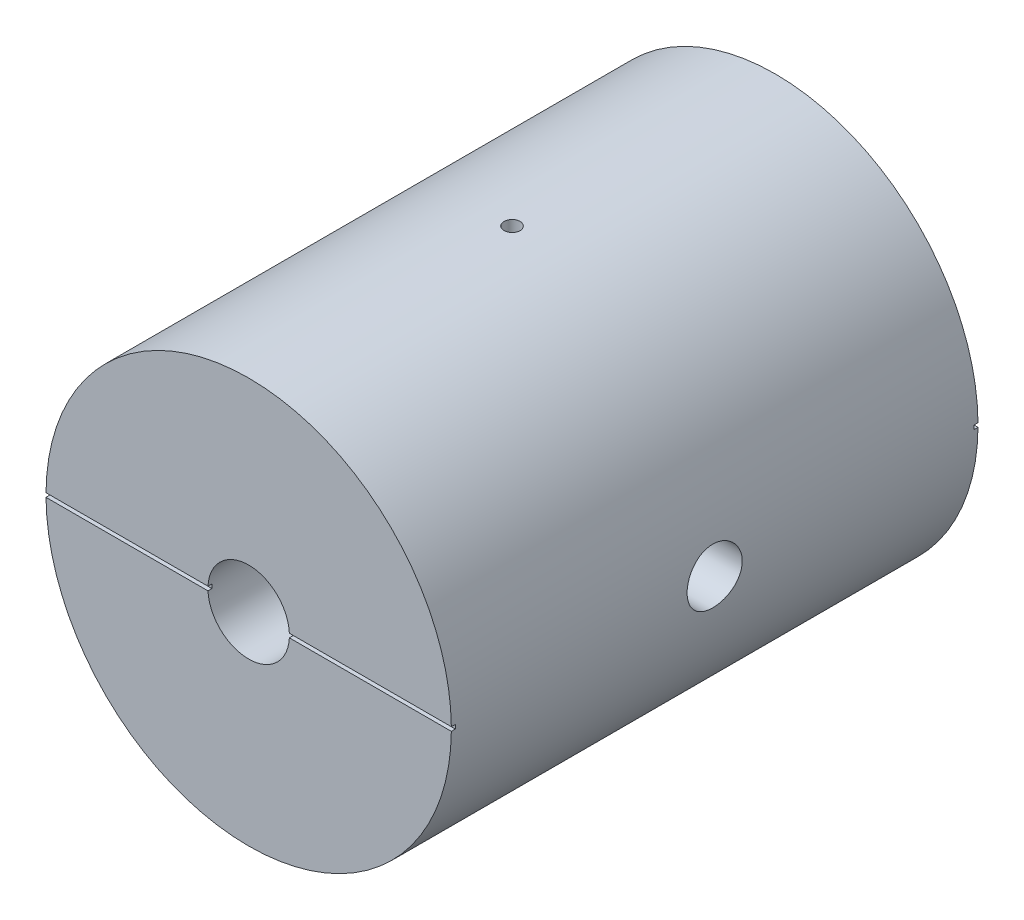
SolidWorks part; units mm, degrees
ref_plane "Front" through (0, 0, 0) normal (0, 0, 1) x (1, 0, 0)
ref_plane "Top" through (0, 0, 0) normal (0, 1, 0) x (1, 0, 0)
ref_plane "Right" through (0, 0, 0) normal (1, 0, 0) x (0, 0, -1)
sketch "Sketch1" plane through (0, 0, 0) normal (0, 0, 1) x (1, 0, 0)
  circle A0 centre (0, 0) radius 12.7
  dimension "D1" = 25.4
extrude "Base-Extrude" add sketch "Sketch1" along normal mid plane 33
hole_wizard "1/4-20 Tapped Hole1" positions "Sketch3" profile "Sketch2" tap size "1/4-20" standard "Ansi Inch"
sketch "Sketch3" plane through (0, 0, 16.5) normal (0, 0, 1) x (1, 0, 0)
  point P0 (0, 0)
cosmetic thread "Cosmetic Thread1" parameters "D1"=6.35, "D2"=6.35
sketch "Sketch2" plane through (0, 0, 16.5) normal (1, 0, 0) x (0, -1, 0)
  line L0 (0, 0) -> (0, 7.8838)
  line L1 (0, 7.8838) -> (2.5527, 6.35)
  line L2 (2.5527, 6.35) -> (2.5527, 0)
  line L5 (2.5527, 0) -> (0, 0)
  line L10 (0, 7.8838) -> (-2.5527, 6.35) construction
  line L11 (0, -6.35) -> (0, 107.95) construction
  dimension "Tap Drill Dia." = 5.1054
  dimension "Tap Drill Depth" = 6.35
  dimension "Drill Angle" = 118
mirror "Mirror1" about plane through (0, 0, 0) normal (0, 0, 1) of "1/4-20 Tapped Hole1"
sketch "Sketch4" plane through (0, 0, 16.5) normal (0, 0, 1) x (1, 0, 0)
  circle A0 centre (0, 0) radius 1.1303
  dimension "D1" = 2.2606
extrude "Cut-Extrude1" cut sketch "Sketch4" against normal through all
ref_plane "Plane1" through (12.7, 0, 0) normal (1, 0, 0) x (0, 0, -1)
hole_wizard "#8-32 Tapped Hole1" positions "Sketch8" profile "Sketch7" tap size "#8-32" standard "Ansi Inch"
sketch "Sketch8" plane through (12.7, 0, 0) normal (1, 0, 0) x (0, 0, -1)
  point P0 (0, 0)
sketch "Sketch7" plane through (12.7, 0, 0) normal (0, 1, 0) x (0, 0, -1)
  line L0 (0, 0) -> (0, 7.3878)
  line L1 (0, 7.3878) -> (1.7272, 6.35)
  line L2 (1.7272, 6.35) -> (1.7272, 0)
  line L5 (1.7272, 0) -> (0, 0)
  line L10 (0, 7.3878) -> (-1.7272, 6.35) construction
  line L11 (0, -6.35) -> (0, 107.95) construction
  dimension "Tap Drill Dia." = 3.4544
  dimension "Tap Drill Depth" = 6.35
  dimension "Drill Angle" = 118
sketch "Sketch9" plane through (12.7, 0, 0) normal (1, 0, 0) x (0, 0, -1)
  circle A0 centre (0, 0) radius 1.1303
  dimension "D1" = 2.2606
extrude "Cut-Extrude2" cut sketch "Sketch9" against normal up to next
sketch "Sketch10" plane through (0, 0, 16.5) normal (0, 0, 1) x (1, 0, 0)
  line L0 (-2.1898, 0) -> (1.877, 0) construction
  line L1 (-13.4517, 0.125) -> (13.8818, 0.125)
  line L2 (-13.4517, 0.125) -> (-13.4517, -0.125)
  line L3 (-13.4517, -0.125) -> (13.8818, -0.125)
  line L4 (13.8818, 0.125) -> (13.8818, -0.125)
  dimension "D1" = 0.25
extrude "Cut-Extrude3" cut sketch "Sketch10" against normal blind 0.25
mirror "Mirror2" about plane through (0, 0, 0) normal (0, 0, 1) of "Cut-Extrude3"
sketch "Sketch11" plane through (0, 0, 0) normal (0, 1, 0) x (1, 0, 0)
  circle A0 centre (0, 0) radius 0.5
  dimension "D1" = 1
extrude "Cut-Extrude4" cut sketch "Sketch11" along normal through all
